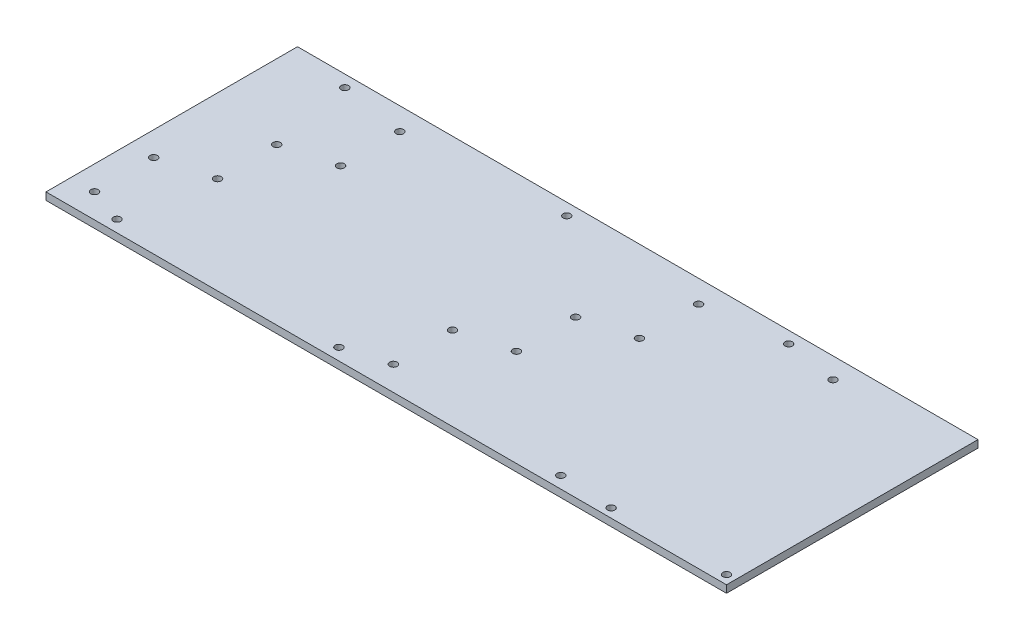
SolidWorks part; units mm, degrees
ref_plane "Ebene vorne" through (0, 0, 0) normal (0, 0, 1) x (1, 0, 0)
ref_plane "Ebene oben" through (0, 0, 0) normal (0, 1, 0) x (1, 0, 0)
ref_plane "Ebene rechts" through (0, 0, 0) normal (1, 0, 0) x (0, 0, -1)
sketch "Skizze1" plane through (0, 0, 0) normal (0, 1, 0) x (1, 0, 0)
  line L1 (-185, -82.5) -> (185, -82.5)
  line L2 (-185, -82.5) -> (-185, 82.5)
  line L3 (-185, 82.5) -> (185, 82.5)
  line L4 (185, -82.5) -> (185, 82.5)
  line L5 (-185, -82.5) -> (185, 82.5) construction
  line L6 (-185, 82.5) -> (185, -82.5) construction
  point P0 (0, 0)
  dimension "D1" = 165
  dimension "D2" = 370
extrude "Aufsatz-Linear austragen1" add sketch "Skizze1" along normal blind 5
hole_wizard "M6 Gewindebohrung1" positions "Skizze3" profile "Skizze4" tap size "M6" standard "DIN" end condition up to next
sketch "Skizze3" plane through (0, 5, 0) normal (0, 1, 0) x (1, 0, 0)
  line L0 (185, 0) -> (-185, 0) construction
  line L1 (185, -82.5) -> (185, 82.5) construction
  line L2 (-185, 82.5) -> (-185, -82.5) construction
  line L4 (67.3, 20) -> (-134.7, 20) construction
  line L5 (67.3, 20) -> (101.3, 69.17) construction
  line L7 (101.3, 69.17) -> (-100.7, 69.17)
  line L8 (101.3, 69.17) -> (101.3, 29.17)
  line L9 (101.3, 29.17) -> (-100.7, 29.17)
  line L10 (-100.7, 69.17) -> (-100.7, 29.17)
  line L11 (67.3, -20) -> (67.3, 20) construction
  line L12 (67.3, -20) -> (33.3, -69.17) construction
  line L15 (33.3, -69.17) -> (-168.7, -69.17)
  line L16 (33.3, -69.17) -> (33.3, -29.17)
  line L17 (33.3, -29.17) -> (-168.7, -29.17)
  line L18 (-168.7, -69.17) -> (-168.7, -29.17)
  point P0 (67.3, -20)
  point P11 (67.3, 20)
  point P18 (-134.7, -20)
  point P19 (-134.7, 20)
  point P28 (101.3, 69.17)
  point P38 (-100.7, 29.17)
  point P117 (101.3, 29.17)
  point P119 (-100.7, 69.17)
  point P129 (33.3, -69.17)
  point P133 (-168.7, -29.17)
  point P272 (33.3, -29.17)
  point P273 (-168.7, -69.17)
  dimension "D1" = 117.7
  dimension "D2" = 20
  dimension "D4" = 202
  dimension "D5" = 34
  dimension "D6" = 49.17
  dimension "D3" = 2
sketch "Skizze4" plane through (67.3, 5, 20) normal (1, 0, 0) x (0, 0, 1)
  line L0 (0, 0) -> (0, 5)
  line L1 (0, 5) -> (2.5, 5)
  line L2 (2.5, 5) -> (2.5, 0)
  line L5 (2.5, 0) -> (0, 0)
  line L11 (0, -6.35) -> (0, 107.95) construction
  dimension "Bohrerdurchmesser" = 5
  dimension "Bohrungstiefe" = 5
cosmetic thread "Bohrungsgewinde1" parameters "D2"=6
cosmetic thread "Bohrungsgewinde2" parameters "D2"=6
cosmetic thread "Bohrungsgewinde3" parameters "D2"=6
cosmetic thread "Bohrungsgewinde4" parameters "D2"=6
cosmetic thread "Bohrungsgewinde5" parameters "D2"=6
cosmetic thread "Bohrungsgewinde6" parameters "D2"=6
cosmetic thread "Bohrungsgewinde7" parameters "D2"=6
cosmetic thread "Bohrungsgewinde8" parameters "D2"=6
cosmetic thread "Bohrungsgewinde9" parameters "D2"=6
cosmetic thread "Bohrungsgewinde10" parameters "D2"=6
cosmetic thread "Bohrungsgewinde11" parameters "D2"=6
cosmetic thread "Bohrungsgewinde12" parameters "D2"=6
sketch "Skizze5" plane through (185, 0, 0) normal (1, 0, 0) x (0, 0, -1)
  line L1 (-82.5, 5) -> (82.5, 5)
  line L2 (-82.5, 5) -> (-82.5, 0)
  line L3 (-82.5, 0) -> (82.5, 0)
  line L4 (82.5, 5) -> (82.5, 0)
extrude "Aufsatz-Linear austragen2" add sketch "Skizze5" along normal blind 90
sketch "Skizze9" plane through (0, 0, 82.5) normal (0, 0, 1) x (1, 0, 0)
  line L1 (-185, 5) -> (275, 5)
  line L2 (-185, 5) -> (-185, 0)
  line L3 (-185, 0) -> (275, 0)
  line L4 (275, 5) -> (275, 0)
extrude "Aufsatz-Linear austragen3" add sketch "Skizze9" along normal blind 3.17
hole_wizard "M6 Gewindebohrung2" positions "Skizze10" profile "Skizze11" tap size "M6" standard "DIN" end condition up to next
sketch "Skizze10" plane through (0, 5, 0) normal (0, 1, 0) x (1, 0, 0)
  line L0 (191, 70.33) -> (191, -79.67) construction
  line L1 (191, -79.67) -> (269, -79.67) construction
  line L3 (275, -85.67) -> (-185, -85.67) construction
  line L4 (185, -82.5) -> (185, 82.5) construction
  line L5 (275, 82.5) -> (275, -85.67) construction
  point P0 (191, 70.33)
  point P2 (191, -79.67)
  point P4 (269, -79.67)
  dimension "D1" = 150
  dimension "D2" = 6
  dimension "D3" = 6
  dimension "D4" = 6
sketch "Skizze11" plane through (191, 5, -70.33) normal (1, 0, 0) x (0, 0, 1)
  line L0 (0, 0) -> (0, 5)
  line L1 (0, 5) -> (2.5, 5)
  line L2 (2.5, 5) -> (2.5, 0)
  line L5 (2.5, 0) -> (0, 0)
  line L11 (0, -6.35) -> (0, 107.95) construction
  dimension "Bohrerdurchmesser" = 5
  dimension "Bohrungstiefe" = 5
cosmetic thread "Bohrungsgewinde13" parameters "D2"=6
cosmetic thread "Bohrungsgewinde14" parameters "D2"=6
cosmetic thread "Bohrungsgewinde15" parameters "D2"=6
sketch "Skizze12" plane through (0, 0, -82.5) normal (0, 0, -1) x (-1, 0, 0)
  line L4 (-275, 0) -> (185, 0)
  line L5 (185, 0) -> (185, 5)
  line L6 (185, 5) -> (-275, 5)
  line L7 (-275, 5) -> (-275, 0)
  line L8 (-275, 0) -> (185, 0)
  line L9 (185, 0) -> (185, 5)
  line L10 (185, 5) -> (-275, 5)
  line L11 (-275, 5) -> (-275, 0)
  dimension "D1" = 0
extrude "Aufsatz-Linear austragen4" add sketch "Skizze12" along normal blind 1.83
hole_wizard "M6 Gewindebohrung3" positions "Skizze13" profile "Skizze14" tap size "M6" standard "DIN" end condition up to next
sketch "Skizze13" plane through (0, 5, 0) normal (0, 1, 0) x (1, 0, 0)
  line L0 (-185, 84.33) -> (-185, -85.67) construction
  line L1 (275, -85.67) -> (-185, -85.67) construction
  line L2 (-185, -0.67) -> (-35.3588, -0.67) construction
  line L5 (-35, -0.67) -> (114.6412, -0.67) construction
  line L6 (115, -0.67) -> (264.6412, -0.67) construction
  point P0 (-145, -77.67)
  point P13 (-145, 76.33)
  point P21 (5, -77.67)
  point P24 (5, 76.33)
  point P25 (155, -77.67)
  point P28 (155, 76.33)
  dimension "D1" = 40
  dimension "D2" = 8
  dimension "D3" = 3
sketch "Skizze14" plane through (-145, 5, 77.67) normal (1, 0, 0) x (0, 0, 1)
  line L0 (0, 0) -> (0, 5)
  line L1 (0, 5) -> (2.5, 5)
  line L2 (2.5, 5) -> (2.5, 0)
  line L5 (2.5, 0) -> (0, 0)
  line L11 (0, -6.35) -> (0, 107.95) construction
  dimension "Bohrerdurchmesser" = 5
  dimension "Bohrungstiefe" = 5
cosmetic thread "Bohrungsgewinde16" parameters "D2"=6
cosmetic thread "Bohrungsgewinde17" parameters "D2"=6
cosmetic thread "Bohrungsgewinde18" parameters "D2"=6
cosmetic thread "Bohrungsgewinde19" parameters "D2"=6
cosmetic thread "Bohrungsgewinde20" parameters "D2"=6
cosmetic thread "Bohrungsgewinde21" parameters "D2"=6
